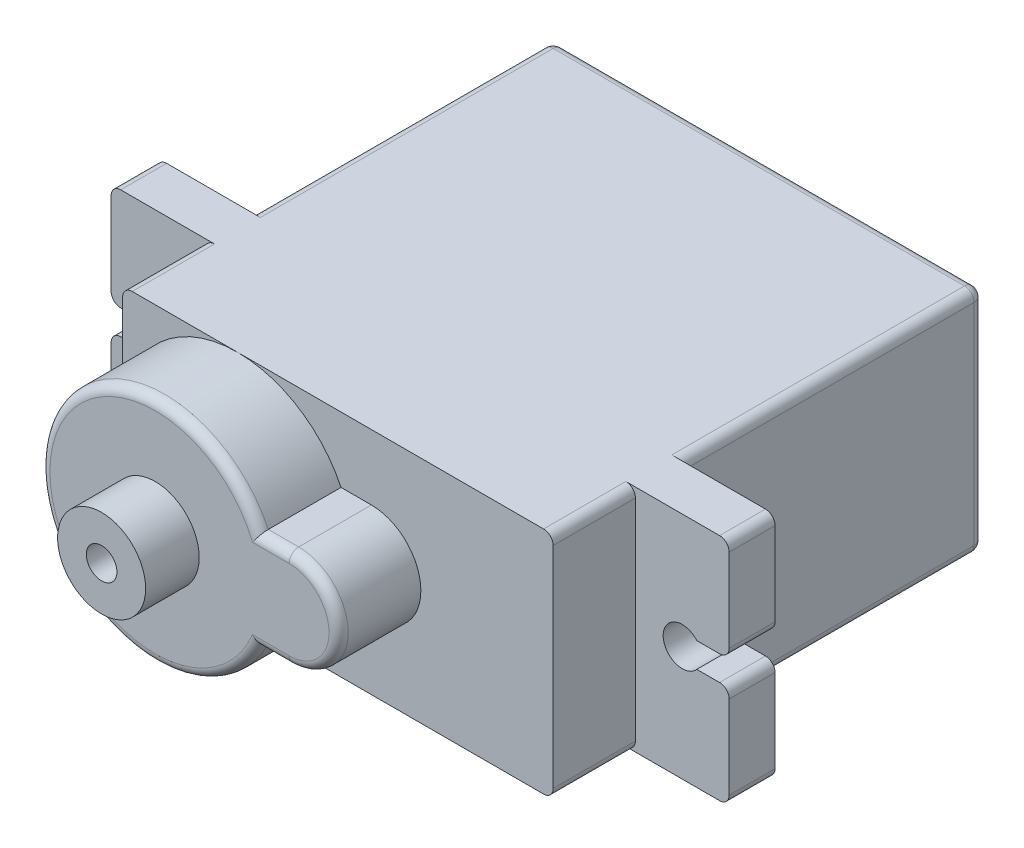
SolidWorks part; units mm, degrees
material "ABS"
ref_plane "Front Plane" through (0, 0, 0) normal (0, 0, 1) x (1, 0, 0)
ref_plane "Top Plane" through (0, 0, 0) normal (0, 1, 0) x (1, 0, 0)
ref_plane "Right Plane" through (0, 0, 0) normal (1, 0, 0) x (0, 0, -1)
sketch "Sketch2" plane through (0, 0, 0) normal (0, 0, 1) x (1, 0, 0)
  line L1 (-15.6538, -2.0258) -> (6.8462, -2.0258)
  line L2 (-15.6538, -2.0258) -> (-15.6538, 9.9742)
  line L3 (-15.6538, 9.9742) -> (6.8462, 9.9742)
  line L4 (6.8462, -2.0258) -> (6.8462, 9.9742)
  dimension "D1" = 12
  dimension "D2" = 22.5
extrude "Boss-Extrude1" add sketch "Sketch2" along normal blind 22.5
sketch "Sketch3" plane through (6.8462, 0, 0) normal (1, 0, 0) x (0, 0, -1)
  line L0 (-22.5, 9.9742) -> (0, 9.9742) construction
  line L1 (-18.2, 9.9742) -> (-15.8, 9.9742)
  line L2 (-18.2, 9.9742) -> (-18.2, -2.0258)
  line L3 (-18.2, -2.0258) -> (-15.8, -2.0258)
  line L4 (-15.8, 9.9742) -> (-15.8, -2.0258)
  line L5 (-22.5, -2.0258) -> (0, -2.0258) construction
  line L6 (-22.5, -2.0258) -> (-22.5, 9.9742) construction
  dimension "D1" = 4.3
  dimension "D2" = 2.4
extrude "Boss-Extrude2" add sketch "Sketch3" along normal blind 4.9 and the other way blind 27.4
sketch "Sketch4" plane through (0, 0, 18.2) normal (0, 0, 1) x (1, 0, 0)
  line L0 (6.8462, 9.9742) -> (11.7462, 9.9742) construction
  line L1 (-20.5538, 9.9742) -> (-15.6538, 9.9742) construction
  line L2 (-20.5538, 9.9742) -> (-20.5538, -2.0258) construction
  circle A0 centre (9.2962, 3.9742) radius 1
  circle A1 centre (-18.1038, 3.9742) radius 1
  point P6 (9.2962, 9.9742)
  point P9 (-18.1038, 9.9742)
  point P12 (-20.5538, 3.9742)
extrude "Cut-Extrude1" cut sketch "Sketch4" against normal up to next
sketch "Sketch5" plane through (0, 0, 22.5) normal (0, 0, 1) x (1, 0, 0)
  circle A0 centre (-9.6538, 3.9742) radius 6
extrude "Boss-Extrude3" add sketch "Sketch5" along normal blind 4.3
sketch "Sketch6" plane through (0, 0, 26.8) normal (0, 0, 1) x (1, 0, 0)
  circle A0 centre (-9.6538, 3.9742) radius 2.3
extrude "Boss-Extrude4" add sketch "Sketch6" along normal blind 2.8
sketch "Sketch7" plane through (0, 0, 29.6) normal (0, 0, 1) x (1, 0, 0)
  circle A0 centre (-9.6538, 3.9742) radius 0.8
extrude "Cut-Extrude2" cut sketch "Sketch7" against normal blind 7
sketch "Sketch8" plane through (0, 0, 18.2) normal (0, 0, 1) x (1, 0, 0)
  line L0 (-20.5538, 9.9742) -> (-20.5538, -2.0258) construction
  line L1 (-22.8879, 4.6242) -> (-18.2197, 4.6242)
  line L2 (-22.8879, 4.6242) -> (-22.8879, 3.3242)
  line L3 (-22.8879, 3.3242) -> (-18.2197, 3.3242)
  line L4 (-18.2197, 4.6242) -> (-18.2197, 3.3242)
  line L5 (-22.8879, 4.6242) -> (-18.2197, 3.3242) construction
  line L6 (-22.8879, 3.3242) -> (-18.2197, 4.6242) construction
  line L7 (11.7462, 9.9742) -> (11.7462, -2.0258) construction
  line L8 (9.6057, 3.3242) -> (13.8866, 3.3242)
  line L9 (9.6057, 3.3242) -> (9.6057, 4.6242)
  line L10 (9.6057, 4.6242) -> (13.8866, 4.6242)
  line L11 (13.8866, 3.3242) -> (13.8866, 4.6242)
  line L12 (9.6057, 3.3242) -> (13.8866, 4.6242) construction
  line L13 (9.6057, 4.6242) -> (13.8866, 3.3242) construction
  point P0 (-20.5538, 3.9742)
  point P7 (11.7462, 3.9742)
  dimension "D1" = 1.3
  dimension "D2" = 1.3
extrude "Cut-Extrude3" cut sketch "Sketch8" against normal up to next
sketch "Sketch9" plane through (0, 0, 22.5) normal (0, 0, 1) x (1, 0, 0)
  line L0 (6.8462, -2.0258) -> (6.8462, 9.9742) construction
  line L1 (-2.6538, 6.5604) -> (-4.2398, 6.5604)
  line L2 (-4.2398, 6.5604) -> (-4.2398, 1.388)
  line L3 (-4.2398, 1.388) -> (-2.6538, 1.388)
  arc A0 (-2.6538, 1.388) -> (-2.6538, 6.5604) centre (-2.6538, 3.9742) ccw
  arc A1 (-9.6538, -2.0258) -> (-9.6538, 9.9742) centre (-9.6538, 3.9742) ccw construction
  point P4 (6.8462, 3.9742)
  point P5 (-3.6538, 3.9742)
  dimension "D1" = 1
extrude "Boss-Extrude6" add sketch "Sketch9" along normal up to surface (4.3 mm away) up to face at (-3.6538, 3.9742, 26.8)
fillet "Fillet1" radius 0.5 24 edges at (-3.4468, 1.388, 26.8) (-0.0676, 3.9742, 26.8) (-4.4038, -2.0258, 0) (6.8462, 3.9742, 0) (-4.4038, 9.9742, 0) (-15.6538, 3.9742, 0) (-3.4468, 6.5604, 26.8) (-15.6538, 3.9742, 26.8) (-20.5538, -2.0258, 17) (-20.5538, 3.3242, 17) (-20.5538, 4.6242, 17) (-20.5538, 9.9742, 17) (11.7462, 9.9742, 17) (11.7462, 4.6242, 17) (11.7462, 3.3242, 17) (11.7462, -2.0258, 17) (6.8462, -2.0258, 20.35) (-15.6538, -2.0258, 20.35) (-15.6538, -2.0258, 7.9) (6.8462, -2.0258, 7.9) (6.8462, 9.9742, 20.35) (-15.6538, 9.9742, 20.35) (-15.6538, 9.9742, 7.9) (6.8462, 9.9742, 7.9)
